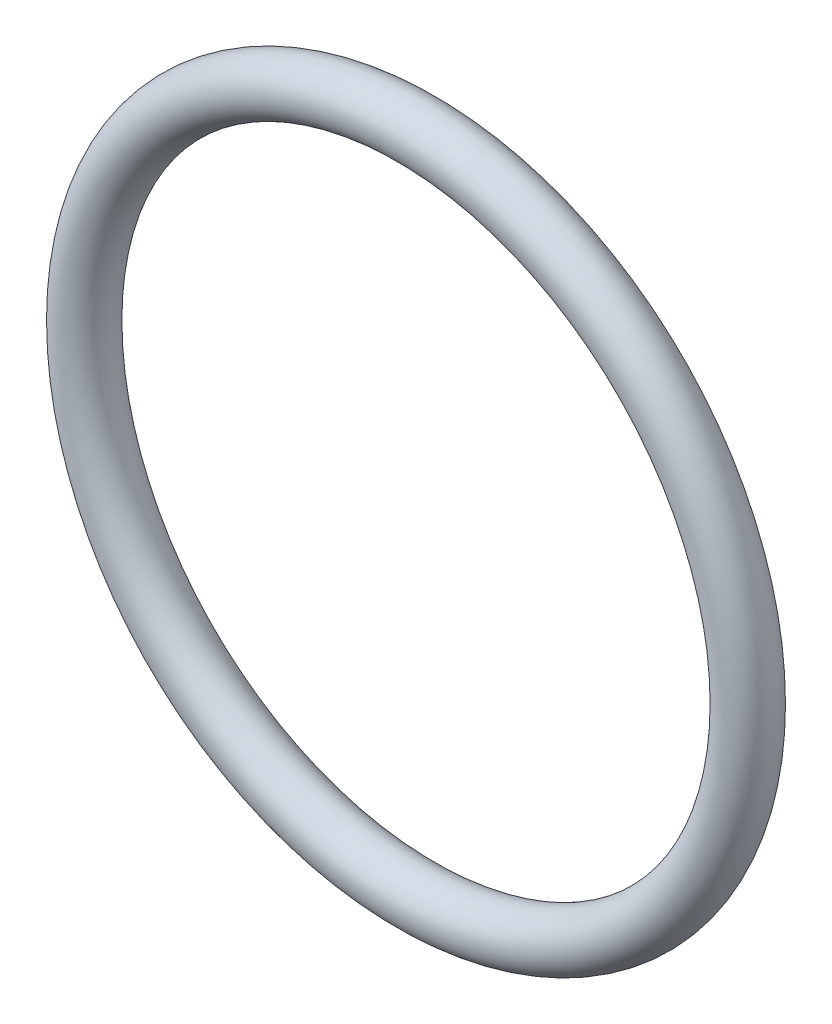
SolidWorks part; units mm, degrees
ref_plane "Front" through (0, 0, 0) normal (0, 0, 1) x (1, 0, 0)
ref_plane "Top" through (0, 0, 0) normal (0, 1, 0) x (1, 0, 0)
ref_plane "Right" through (0, 0, 0) normal (1, 0, 0) x (0, 0, -1)
sketch "Sketch1" plane through (0, 0, 0) normal (1, 0, 0) x (0, -1, 0)
  line L0 (0, -0.889) -> (0, 0.889) construction
  line L2 (-13.1458, 0) -> (13.1458, 0) construction
  line L3 (-10.1727, 0) -> (10.1727, 0) construction
  circle A0 centre (11.0617, 0) radius 0.889
  point P9 (10.1727, 0)
  point P10 (11.9507, 0)
  point P13 (11.0617, 0.889)
  point P14 (11.0617, -0.889)
  dimension "Width" = 1.778
  dimension "ID" = 20.3454
revolve "Revolve1" add sketch "Sketch1" angle 360 about L0
